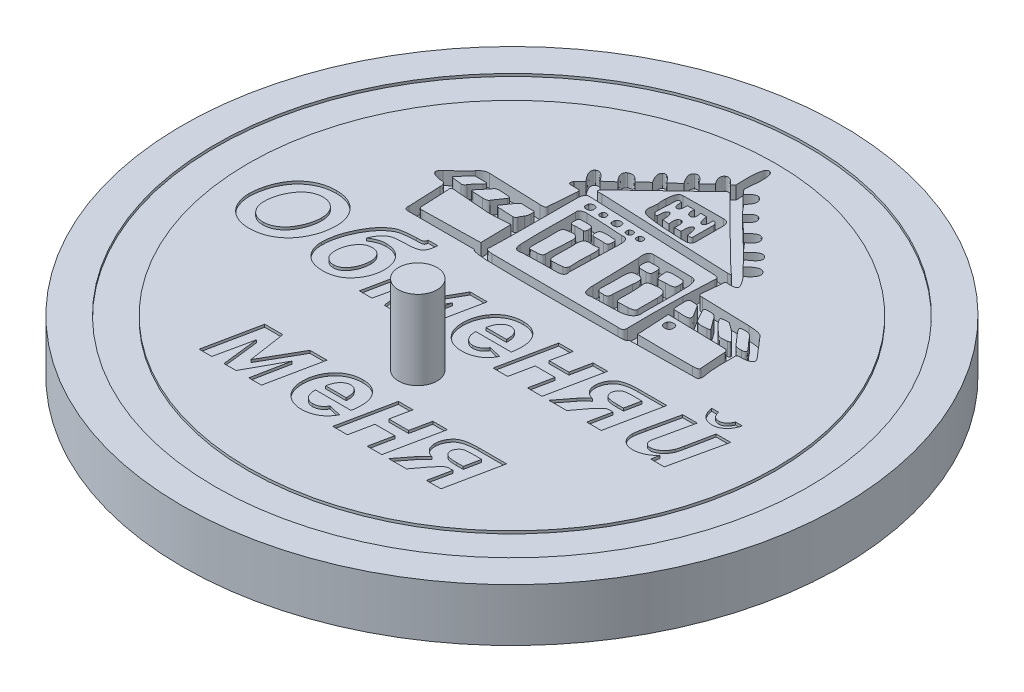
SolidWorks part; units mm, degrees
ref_plane "Спереди" through (0, 0, 0) normal (0, 0, 1) x (1, 0, 0)
ref_plane "Сверху" through (0, 0, 0) normal (0, 1, 0) x (1, 0, 0)
ref_plane "Справа" through (0, 0, 0) normal (1, 0, 0) x (0, 0, -1)
sketch "Эскиз1" plane through (0, 0, 0) normal (0, 1, 0) x (1, 0, 0)
  circle A0 centre (0, 0) radius 25
  dimension "D1" = 50
extrude "Бобышка-Вытянуть1" add sketch "Эскиз1" along normal blind 4
sketch "Эскиз2" plane through (0, 4, 0) normal (0, 1, 0) x (1, 0, 0)
  circle A0 centre (0, 0) radius 22.5
  circle A1 centre (0, 0) radius 20
  dimension "D1" = 45
  dimension "D2" = 40
extrude "Вырез-Вытянуть1" cut sketch "Эскиз2" against normal blind 0.2
sketch "Эскиз3" plane through (0, 4, 0) normal (0, 1, 0) x (1, 0, 0)
  text T0 "<b>Обменяй </b>\r\n<b>    меня</b>" font "Arial" height in points 22
extrude "Вырез-Вытянуть2" cut sketch "Эскиз3" against normal blind 0.2
sketch "Эскиз4" plane through (0, 4, 0) normal (0, 1, 0) x (1, 0, 0)
  line B0 (6.0558, 2.8211) -> (10.9499, 2.8913)
  line B1 (5.5647, 11.9601) -> (5.135, 12.46)
  line B2 (4.6263, 12.9249) -> (4.0299, 13.6177)
  line B3 (3.3984, 14.1615) -> (2.6617, 14.8719)
  line B4 (2.1004, 15.3718) -> (1.4776, 16.0998)
  line B5 (0.8198, 16.7226) -> (0.4953, 17.0997)
  line B6 (-0.0835, 17.0821) -> (-0.3116, 16.8804)
  line B7 (-0.9255, 16.3629) -> (-1.557, 15.7402)
  line B8 (-2.1534, 15.2052) -> (-2.8463, 14.5913)
  line B9 (-3.4252, 14.0826) -> (-4.1268, 13.4599)
  line B10 (-4.767, 12.8021) -> (-5.495, 12.1706)
  line B11 (-5.9949, 11.6093) -> (-6.451, 11.162)
  line B12 (-9.6874, 6.8425) -> (-9.0427, 7.6274)
  line B13 (-7.6701, 6.5969) -> (-6.4422, 6.5311)
  line B14 (5.9946, 3.536) -> (5.8542, 6.0093)
  line B15 (5.8542, 6.0093) -> (10.3097, 5.904)
  line B16 (-10.6872, 5.8426) -> (-10.5907, 3.7026)
  line B17 (-5.9774, 3.6149) -> (-6.0212, 5.9478)
  line B18 (-0.5858, 12.0196) -> (-0.0683, 11.9757)
  line B19 (0.3702, 11.9318) -> (0.8702, 11.9494)
  line B20 (0.8965, 13.8701) -> (0.4316, 13.8789)
  line B21 (-0.0332, 13.8789) -> (-0.5682, 13.8701)
  line B22 (-3.5064, 8.2833) -> (-2.8661, 8.2833)
  spline B23 degree 2 poles (-11.6257, 6.2066) (-11.2047, 6.2416) (-11.2047, 5.7505) knots 0 0 0 0.015873 0.015873 0.015873
  spline B24 degree 2 poles (-11.2047, 5.7505) (-11.2047, 5.2593) (-11.0994, 3.2947) knots 0.015873 0.015873 0.015873 0.031746 0.031746 0.031746
  spline B25 degree 2 poles (-11.0994, 3.2947) (-11.1696, 2.9088) (-10.7662, 2.9263) knots 0.031746 0.031746 0.031746 0.047619 0.047619 0.047619
  spline B26 degree 2 poles (-10.7662, 2.9263) (-10.3627, 2.9439) (-5.7494, 2.9263) knots 0.047619 0.047619 0.047619 0.063492 0.063492 0.063492
  spline B27 degree 2 poles (-5.7494, 2.9263) (-5.802, 2.7509) (-4.6267, 2.6808) knots 0.063492 0.063492 0.063492 0.079365 0.079365 0.079365
  spline B28 degree 2 poles (-4.6267, 2.6808) (-3.4515, 2.6106) (5.5121, 2.6457) knots 0.079365 0.079365 0.079365 0.095238 0.095238 0.095238
  spline B29 degree 2 poles (5.5121, 2.6457) (6.0383, 2.6281) (6.0558, 2.8211) knots 0.095238 0.095238 0.095238 0.111111 0.111111 0.111111
  spline B30 degree 2 poles (10.9499, 2.8913) (11.3884, 2.8211) (11.2481, 3.4526) knots 0.126984 0.126984 0.126984 0.142857 0.142857 0.142857
  spline B31 degree 2 poles (11.2481, 3.4526) (11.1077, 4.0841) (11.1428, 5.6453) knots 0.142857 0.142857 0.142857 0.15873 0.15873 0.15873
  spline B32 degree 2 poles (11.1428, 5.6453) (11.0551, 5.9347) (11.3358, 5.9259) knots 0.15873 0.15873 0.15873 0.174603 0.174603 0.174603
  spline B33 degree 3 poles (11.3358, 5.9259) (11.6164, 5.9171) (12.5636, 5.9698) (12.0901, 6.5135) knots 0.174603 0.174603 0.174603 0.174603 0.190476 0.190476 0.190476 0.190476
  spline B34 degree 2 poles (12.0901, 6.5135) (11.6164, 7.0573) (10.8359, 7.9695) knots 0.190476 0.190476 0.190476 0.206349 0.206349 0.206349
  spline B35 degree 2 poles (10.8359, 7.9695) (10.7131, 8.2852) (9.6606, 8.3203) knots 0.206349 0.206349 0.206349 0.222222 0.222222 0.222222
  spline B36 degree 2 poles (9.6606, 8.3203) (8.6081, 8.3554) (6.012, 8.4255) knots 0.222222 0.222222 0.222222 0.238095 0.238095 0.238095
  spline B37 degree 2 poles (6.012, 8.4255) (5.7226, 8.3729) (5.7401, 8.6711) knots 0.238095 0.238095 0.238095 0.253968 0.253968 0.253968
  spline B38 degree 2 poles (5.7401, 8.6711) (5.7577, 8.9693) (5.8893, 10.1797) knots 0.253968 0.253968 0.253968 0.269841 0.269841 0.269841
  spline B39 degree 2 poles (5.8893, 10.1797) (5.8717, 10.2937) (6.0384, 10.2937) knots 0.269841 0.269841 0.269841 0.285714 0.285714 0.285714
  spline B40 degree 3 poles (6.0384, 10.2937) (6.205, 10.2937) (6.9943, 10.1797) (6.6698, 10.6971) knots 0.285714 0.285714 0.285714 0.285714 0.301587 0.301587 0.301587 0.301587
  spline B41 degree 2 poles (6.6698, 10.6971) (6.3453, 11.2146) (6.205, 11.3286) knots 0.301587 0.301587 0.301587 0.31746 0.31746 0.31746
  spline B42 degree 2 poles (6.205, 11.3286) (7.0294, 11.9864) (6.6786, 12.3635) knots 0.31746 0.31746 0.31746 0.333333 0.333333 0.333333
  spline B43 degree 2 poles (6.6786, 12.3635) (6.3278, 12.7406) (5.5647, 11.9601) knots 0.333333 0.333333 0.333333 0.349206 0.349206 0.349206
  spline B44 degree 2 poles (5.135, 12.46) (6.091, 13.0389) (5.7401, 13.4248) knots 0.365079 0.365079 0.365079 0.380952 0.380952 0.380952
  spline B45 degree 2 poles (5.7401, 13.4248) (5.3893, 13.8106) (4.6263, 12.9249) knots 0.380952 0.380952 0.380952 0.396825 0.396825 0.396825
  spline B46 degree 2 poles (4.0299, 13.6177) (4.7754, 14.1176) (4.4246, 14.5386) knots 0.412698 0.412698 0.412698 0.428571 0.428571 0.428571
  spline B47 degree 2 poles (4.4246, 14.5386) (4.0737, 14.9596) (3.3984, 14.1615) knots 0.428571 0.428571 0.428571 0.444444 0.444444 0.444444
  spline B48 degree 2 poles (2.6617, 14.8719) (3.3019, 15.4332) (2.9774, 15.7577) knots 0.460317 0.460317 0.460317 0.47619 0.47619 0.47619
  spline B49 degree 2 poles (2.9774, 15.7577) (2.6529, 16.0823) (2.1004, 15.3718) knots 0.47619 0.47619 0.47619 0.492063 0.492063 0.492063
  spline B50 degree 2 poles (1.4776, 16.0998) (2.0565, 16.6348) (1.7408, 17.0383) knots 0.507937 0.507937 0.507937 0.52381 0.52381 0.52381
  spline B51 degree 2 poles (1.7408, 17.0383) (1.425, 17.4417) (0.8198, 16.7226) knots 0.52381 0.52381 0.52381 0.539683 0.539683 0.539683
  spline B52 degree 2 poles (0.4953, 17.0997) (0.776, 19.1871) (0.2848, 19.2572) knots 0.555556 0.555556 0.555556 0.571429 0.571429 0.571429
  spline B53 degree 2 poles (0.2848, 19.2572) (-0.2063, 19.3274) (-0.0835, 17.0821) knots 0.571429 0.571429 0.571429 0.587302 0.587302 0.587302
  spline B54 degree 2 poles (-0.3116, 16.8804) (-0.7852, 17.468) (-1.0834, 17.2312) knots 0.603175 0.603175 0.603175 0.619048 0.619048 0.619048
  spline B55 degree 2 poles (-1.0834, 17.2312) (-1.3816, 16.9944) (-0.9255, 16.3629) knots 0.619048 0.619048 0.619048 0.634921 0.634921 0.634921
  spline B56 degree 2 poles (-1.557, 15.7402) (-2.0482, 16.4857) (-2.3902, 16.2401) knots 0.650794 0.650794 0.650794 0.666667 0.666667 0.666667
  spline B57 degree 2 poles (-2.3902, 16.2401) (-2.7323, 15.9946) (-2.1534, 15.2052) knots 0.666667 0.666667 0.666667 0.68254 0.68254 0.68254
  spline B58 degree 2 poles (-2.8463, 14.5913) (-3.355, 15.2929) (-3.6356, 15.0649) knots 0.698413 0.698413 0.698413 0.714286 0.714286 0.714286
  spline B59 degree 2 poles (-3.6356, 15.0649) (-3.9163, 14.8368) (-3.4252, 14.0826) knots 0.714286 0.714286 0.714286 0.730159 0.730159 0.730159
  spline B60 degree 2 poles (-4.1268, 13.4599) (-4.6004, 14.0299) (-5.0039, 13.7581) knots 0.746032 0.746032 0.746032 0.761905 0.761905 0.761905
  spline B61 degree 2 poles (-5.0039, 13.7581) (-5.4073, 13.4862) (-4.767, 12.8021) knots 0.761905 0.761905 0.761905 0.777778 0.777778 0.777778
  spline B62 degree 2 poles (-5.495, 12.1706) (-6.0388, 12.9775) (-6.3896, 12.7144) knots 0.793651 0.793651 0.793651 0.809524 0.809524 0.809524
  spline B63 degree 2 poles (-6.3896, 12.7144) (-6.7405, 12.4513) (-5.9949, 11.6093) knots 0.809524 0.809524 0.809524 0.825397 0.825397 0.825397
  spline B64 degree 2 poles (-6.451, 11.162) (-6.6615, 10.8287) (-6.3107, 10.8199) knots 0.84127 0.84127 0.84127 0.857143 0.857143 0.857143
  spline B65 degree 2 poles (-6.3107, 10.8199) (-5.9599, 10.8111) (-5.7494, 10.8111) knots 0.857143 0.857143 0.857143 0.873016 0.873016 0.873016
  spline B66 degree 2 poles (-5.7494, 10.8111) (-5.6178, 10.7936) (-5.6441, 10.5656) knots 0.873016 0.873016 0.873016 0.888889 0.888889 0.888889
  spline B67 degree 2 poles (-5.6441, 10.5656) (-5.6705, 10.3375) (-5.8108, 8.5483) knots 0.888889 0.888889 0.888889 0.904762 0.904762 0.904762
  spline B68 degree 2 poles (-5.8108, 8.5483) (-5.7581, 8.3203) (-6.2318, 8.3554) knots 0.904762 0.904762 0.904762 0.920635 0.920635 0.920635
  spline B69 degree 2 poles (-6.2318, 8.3554) (-6.7054, 8.3905) (-10.2136, 8.5045) knots 0.920635 0.920635 0.920635 0.936508 0.936508 0.936508
  spline B70 degree 2 poles (-10.2136, 8.5045) (-10.6171, 8.5132) (-10.9065, 8.1273) knots 0.936508 0.936508 0.936508 0.952381 0.952381 0.952381
  spline B71 degree 2 poles (-10.9065, 8.1273) (-11.1959, 7.7414) (-12.1607, 6.9257) knots 0.952381 0.952381 0.952381 0.968254 0.968254 0.968254
  spline B72 degree 2 poles (-12.1607, 6.9257) (-12.7571, 6.3644) (-11.6257, 6.2066) knots 0.968254 0.968254 0.968254 1 1 1
  spline B73 degree 2 poles (-11.2573, 7.0222) (-11.4854, 6.8424) (-11.2793, 6.8074) knots 0 0 0 0.111111 0.111111 0.111111
  spline B74 degree 2 poles (-11.2793, 6.8074) (-11.0731, 6.7723) (-10.5951, 6.7284) knots 0.111111 0.111111 0.111111 0.222222 0.222222 0.222222
  spline B75 degree 2 poles (-10.5951, 6.7284) (-10.446, 6.6802) (-10.3013, 6.9082) knots 0.222222 0.222222 0.222222 0.333333 0.333333 0.333333
  spline B76 degree 2 poles (-10.3013, 6.9082) (-10.1566, 7.1363) (-9.7532, 7.5572) knots 0.333333 0.333333 0.333333 0.444444 0.444444 0.444444
  spline B77 degree 2 poles (-9.7532, 7.5572) (-9.547, 7.7546) (-9.7575, 7.7678) knots 0.444444 0.444444 0.444444 0.555556 0.555556 0.555556
  spline B78 degree 2 poles (-9.7575, 7.7678) (-9.968, 7.7809) (-10.4592, 7.7721) knots 0.555556 0.555556 0.555556 0.666667 0.666667 0.666667
  spline B79 degree 2 poles (-10.4592, 7.7721) (-10.5381, 7.8072) (-10.6477, 7.7063) knots 0.666667 0.666667 0.666667 0.777778 0.777778 0.777778
  spline B80 degree 2 poles (-10.6477, 7.7063) (-10.7574, 7.6055) (-11.2573, 7.0222) knots 0.777778 0.777778 0.777778 1 1 1
  spline B81 degree 2 poles (-9.0427, 7.6274) (-8.9945, 7.7458) (-8.7139, 7.7546) knots 0.111111 0.111111 0.111111 0.222222 0.222222 0.222222
  spline B82 degree 2 poles (-8.7139, 7.7546) (-8.4332, 7.7634) (-8.0692, 7.7151) knots 0.222222 0.222222 0.222222 0.333333 0.333333 0.333333
  spline B83 degree 2 poles (-8.0692, 7.7151) (-7.7491, 7.7107) (-7.8806, 7.5266) knots 0.333333 0.333333 0.333333 0.444444 0.444444 0.444444
  spline B84 degree 2 poles (-7.8806, 7.5266) (-8.0122, 7.3424) (-8.4112, 6.7504) knots 0.444444 0.444444 0.444444 0.555556 0.555556 0.555556
  spline B85 degree 2 poles (-8.4112, 6.7504) (-8.442, 6.61) (-8.8322, 6.6144) knots 0.555556 0.555556 0.555556 0.666667 0.666667 0.666667
  spline B86 degree 2 poles (-8.8322, 6.6144) (-9.2225, 6.6188) (-9.6216, 6.6539) knots 0.666667 0.666667 0.666667 0.777778 0.777778 0.777778
  spline B87 degree 2 poles (-9.6216, 6.6539) (-9.8584, 6.6758) (-9.6874, 6.8425) knots 0.777778 0.777778 0.777778 1 1 1
  spline B88 degree 2 poles (-6.4422, 6.5311) (-6.2887, 6.5618) (-6.2405, 6.6934) knots 0.1 0.1 0.1 0.2 0.2 0.2
  spline B89 degree 2 poles (-6.2405, 6.6934) (-6.1923, 6.8249) (-6.0607, 7.0222) knots 0.2 0.2 0.2 0.3 0.3 0.3
  spline B90 degree 2 poles (-6.0607, 7.0222) (-5.9642, 7.1977) (-5.9599, 7.395) knots 0.3 0.3 0.3 0.4 0.4 0.4
  spline B91 degree 3 poles (-5.9599, 7.395) (-5.9555, 7.5923) (-5.8941, 7.7107) (-6.1528, 7.6976) knots 0.4 0.4 0.4 0.4 0.5 0.5 0.5 0.5
  spline B92 degree 2 poles (-6.1528, 7.6976) (-6.4116, 7.6844) (-6.9246, 7.7195) knots 0.5 0.5 0.5 0.6 0.6 0.6
  spline B93 degree 2 poles (-6.9246, 7.7195) (-7.0167, 7.7502) (-7.1439, 7.6099) knots 0.6 0.6 0.6 0.7 0.7 0.7
  spline B94 degree 2 poles (-7.1439, 7.6099) (-7.2711, 7.4696) (-7.7447, 6.7591) knots 0.7 0.7 0.7 0.8 0.8 0.8
  spline B95 degree 2 poles (-7.7447, 6.7591) (-7.8192, 6.6363) (-7.6701, 6.5969) knots 0.8 0.8 0.8 1 1 1
  spline B96 degree 3 poles (6.0799, 6.538) (6.571, 6.5157) (7.2003, 6.3978) (6.8254, 6.9765) knots 0 0 0 0 0.166667 0.166667 0.166667 0.166667
  spline B97 degree 3 poles (6.8254, 6.9765) (6.4792, 7.5109) (6.5009, 7.5027) (6.4395, 7.5992) knots 0.166667 0.166667 0.166667 0.166667 0.333333 0.333333 0.333333 0.333333
  spline B98 degree 3 poles (6.4395, 7.5992) (6.3781, 7.6957) (6.3781, 7.7308) (6.0799, 7.7395) knots 0.333333 0.333333 0.333333 0.333333 0.5 0.5 0.5 0.5
  spline B99 degree 3 poles (6.0799, 7.7395) (5.7356, 7.7497) (5.615, 7.8845) (5.6451, 7.1604) knots 0.5 0.5 0.5 0.5 0.666667 0.666667 0.666667 0.666667
  spline B100 degree 3 poles (5.6451, 7.1604) (5.676, 6.419) (5.6735, 6.5564) (6.0799, 6.538) knots 0.666667 0.666667 0.666667 0.666667 1 1 1 1
  spline B101 degree 3 poles (7.1587, 7.0861) (7.0857, 7.2532) (6.956, 7.3736) (6.8829, 7.6243) knots 0 0 0 0 0.111111 0.111111 0.111111 0.111111
  spline B102 degree 3 poles (6.8829, 7.6243) (6.8553, 7.7188) (6.931, 7.7486) (7.0798, 7.7571) knots 0.111111 0.111111 0.111111 0.111111 0.222222 0.222222 0.222222 0.222222
  spline B103 degree 3 poles (7.0798, 7.7571) (7.3868, 7.7746) (7.3868, 7.7395) (7.492, 7.7308) knots 0.222222 0.222222 0.222222 0.222222 0.333333 0.333333 0.333333 0.333333
  spline B104 degree 3 poles (7.492, 7.7308) (7.5972, 7.722) (7.6674, 7.722) (7.9481, 7.3186) knots 0.333333 0.333333 0.333333 0.333333 0.444444 0.444444 0.444444 0.444444
  spline B105 degree 2 poles (7.9481, 7.3186) (8.2287, 6.9151) (8.3691, 6.7485) knots 0.444444 0.444444 0.444444 0.555556 0.555556 0.555556
  spline B106 degree 2 poles (8.3691, 6.7485) (8.562, 6.5731) (8.2375, 6.5467) knots 0.555556 0.555556 0.555556 0.666667 0.666667 0.666667
  spline B107 degree 3 poles (8.2375, 6.5467) (8.0005, 6.5275) (7.7297, 6.5102) (7.5924, 6.5591) knots 0.666667 0.666667 0.666667 0.666667 0.777778 0.777778 0.777778 0.777778
  spline B108 degree 3 poles (7.5924, 6.5591) (7.4028, 6.6265) (7.3148, 6.7562) (7.1587, 7.0861) knots 0.777778 0.777778 0.777778 0.777778 1 1 1 1
  spline B109 degree 3 poles (8.1207, 7.6044) (8.0402, 7.7449) (8.169, 7.7427) (8.3427, 7.7658) knots 0 0 0 0 0.142857 0.142857 0.142857 0.142857
  spline B110 degree 2 poles (8.3427, 7.7658) (8.7374, 7.8185) (8.7725, 7.7308) knots 0.142857 0.142857 0.142857 0.285714 0.285714 0.285714
  spline B111 degree 2 poles (8.7725, 7.7308) (9.2637, 7.4063) (9.6145, 7.0554) knots 0.285714 0.285714 0.285714 0.428571 0.428571 0.428571
  spline B112 degree 3 poles (9.6145, 7.0554) (9.9653, 6.7046) (10.1714, 6.5174) (9.8688, 6.4941) knots 0.428571 0.428571 0.428571 0.428571 0.571429 0.571429 0.571429 0.571429
  spline B113 degree 3 poles (9.8688, 6.4941) (9.4039, 6.4583) (9.2888, 6.3801) (8.9884, 6.6721) knots 0.571429 0.571429 0.571429 0.571429 0.714286 0.714286 0.714286 0.714286
  spline B114 degree 3 poles (8.9884, 6.6721) (8.6449, 7.0061) (8.3252, 7.2481) (8.1207, 7.6044) knots 0.714286 0.714286 0.714286 0.714286 1 1 1 1
  spline B115 degree 3 poles (9.5095, 7.8173) (9.632, 7.8792) (10.0231, 7.8626) (10.1326, 7.8217) knots 0 0 0 0 0.166667 0.166667 0.166667 0.166667
  spline B116 degree 3 poles (10.1326, 7.8217) (10.3502, 7.7403) (10.5713, 7.4128) (10.7284, 7.2221) knots 0.166667 0.166667 0.166667 0.166667 0.333333 0.333333 0.333333 0.333333
  spline B117 degree 3 poles (10.7284, 7.2221) (10.9739, 6.9239) (11.5923, 6.459) (11.0003, 6.4239) knots 0.333333 0.333333 0.333333 0.333333 0.5 0.5 0.5 0.5
  spline B118 degree 3 poles (11.0003, 6.4239) (10.4082, 6.3889) (10.3364, 6.6793) (10.2591, 6.7748) knots 0.5 0.5 0.5 0.5 0.666667 0.666667 0.666667 0.666667
  spline B119 degree 3 poles (10.2591, 6.7748) (10.1819, 6.8702) (9.3192, 7.721) (9.5095, 7.8173) knots 0.666667 0.666667 0.666667 0.666667 1 1 1 1
  spline B120 degree 2 poles (-5.3108, 3.6061) (-5.4161, 3.3342) (-4.8021, 3.3079) knots 0 0 0 0.1 0.1 0.1
  spline B121 degree 2 poles (-4.8021, 3.3079) (-4.1882, 3.2816) (4.8017, 3.2553) knots 0.1 0.1 0.1 0.2 0.2 0.2
  spline B122 degree 2 poles (4.8017, 3.2553) (5.2402, 3.1851) (5.2052, 3.571) knots 0.2 0.2 0.2 0.3 0.3 0.3
  spline B123 degree 3 poles (5.2052, 3.571) (5.1701, 3.9569) (5.1876, 6.974) (5.2227, 7.7634) knots 0.3 0.3 0.3 0.3 0.4 0.4 0.4 0.4
  spline B124 degree 2 poles (5.2227, 7.7634) (5.2578, 8.5527) (5.328, 10.0613) knots 0.4 0.4 0.4 0.5 0.5 0.5
  spline B125 degree 2 poles (5.328, 10.0613) (5.4157, 10.3419) (4.9596, 10.3595) knots 0.5 0.5 0.5 0.6 0.6 0.6
  spline B126 degree 2 poles (4.9596, 10.3595) (4.5035, 10.377) (-4.8109, 10.7629) knots 0.6 0.6 0.6 0.7 0.7 0.7
  spline B127 degree 2 poles (-4.8109, 10.7629) (-5.2319, 10.8331) (-5.2494, 10.1841) knots 0.7 0.7 0.7 0.8 0.8 0.8
  spline B128 degree 3 poles (-5.2494, 10.1841) (-5.267, 9.535) (-5.2319, 4.8866) (-5.3108, 3.6061) knots 0.8 0.8 0.8 0.8 1 1 1 1
  spline B129 degree 2 poles (-4.5676, 11.4056) (-5.164, 11.3004) (-4.8307, 11.6687) knots 0 0 0 0.142857 0.142857 0.142857
  spline B130 degree 2 poles (-4.8307, 11.6687) (-4.4974, 12.0371) (-0.1121, 16.1593) knots 0.142857 0.142857 0.142857 0.285714 0.285714 0.285714
  spline B131 degree 2 poles (-0.1121, 16.1593) (0.0984, 16.4926) (0.379, 16.1593) knots 0.285714 0.285714 0.285714 0.428571 0.428571 0.428571
  spline B132 degree 2 poles (0.379, 16.1593) (0.6597, 15.826) (5.4309, 11.1776) knots 0.428571 0.428571 0.428571 0.571429 0.571429 0.571429
  spline B133 degree 2 poles (5.4309, 11.1776) (5.7817, 10.9671) (5.3783, 10.9671) knots 0.571429 0.571429 0.571429 0.714286 0.714286 0.714286
  spline B134 degree 2 poles (5.3783, 10.9671) (4.9748, 10.9671) (-4.5676, 11.4056) knots 0.714286 0.714286 0.714286 1 1 1
  spline B135 degree 2 poles (10.3097, 5.904) (10.4851, 5.8339) (10.4851, 5.6409) knots 0.285714 0.285714 0.285714 0.428571 0.428571 0.428571
  spline B136 degree 2 poles (10.4851, 5.6409) (10.4851, 5.448) (10.6255, 3.7289) knots 0.428571 0.428571 0.428571 0.571429 0.571429 0.571429
  spline B137 degree 2 poles (10.6255, 3.7289) (10.6956, 3.5184) (10.1694, 3.5184) knots 0.571429 0.571429 0.571429 0.714286 0.714286 0.714286
  spline B138 degree 3 poles (10.1694, 3.5184) (9.6431, 3.5184) (6.6962, 3.4834) (5.9946, 3.536) knots 0.714286 0.714286 0.714286 0.714286 1 1 1 1
  spline B139 degree 2 poles (-10.5907, 3.7026) (-10.5907, 3.5359) (-10.3363, 3.5272) knots 0.125 0.125 0.125 0.25 0.25 0.25
  spline B140 degree 2 poles (-10.3363, 3.5272) (-10.082, 3.5184) (-5.9774, 3.6149) knots 0.25 0.25 0.25 0.375 0.375 0.375
  spline B141 degree 2 poles (-6.0212, 5.9478) (-7.1702, 5.8426) (-7.7052, 5.8601) knots 0.5 0.5 0.5 0.625 0.625 0.625
  spline B142 degree 3 poles (-7.7052, 5.8601) (-8.2402, 5.8777) (-10.1347, 6.0443) (-10.2487, 6.0618) knots 0.625 0.625 0.625 0.625 0.75 0.75 0.75 0.75
  spline B143 degree 3 poles (-10.2487, 6.0618) (-10.3627, 6.0794) (-10.7837, 6.1846) (-10.6872, 5.8426) knots 0.75 0.75 0.75 0.75 1 1 1 1
  spline B144 degree 2 poles (6.3103, 5.448) (6.17, 4.9743) (6.6261, 4.9743) knots 0 0 0 0.25 0.25 0.25
  spline B145 degree 3 poles (6.6261, 4.9743) (7.0821, 4.9743) (6.9769, 5.5006) (6.8453, 5.5795) knots 0.25 0.25 0.25 0.25 0.5 0.5 0.5 0.5
  spline B146 degree 3 poles (6.8453, 5.5795) (6.7137, 5.6584) (6.3805, 5.6584) (6.3103, 5.448) knots 0.5 0.5 0.5 0.5 1 1 1 1
  spline B147 degree 2 poles (-0.3879, 10.0048) (-0.4848, 9.6777) (-0.1698, 9.6777) knots 0 0 0 0.25 0.25 0.25
  spline B148 degree 3 poles (-0.1698, 9.6777) (0.1452, 9.6777) (0.0725, 10.0411) (-0.0183, 10.0957) knots 0.25 0.25 0.25 0.25 0.5 0.5 0.5 0.5
  spline B149 degree 3 poles (-0.0183, 10.0957) (-0.1092, 10.1502) (-0.3394, 10.1502) (-0.3879, 10.0048) knots 0.5 0.5 0.5 0.5 1 1 1 1
  spline B150 degree 2 poles (-1.1948, 10.0223) (-1.2917, 9.6952) (-0.9767, 9.6952) knots 0 0 0 0.25 0.25 0.25
  spline B151 degree 3 poles (-0.9767, 9.6952) (-0.6617, 9.6952) (-0.7344, 10.0587) (-0.8252, 10.1132) knots 0.25 0.25 0.25 0.25 0.5 0.5 0.5 0.5
  spline B152 degree 3 poles (-0.8252, 10.1132) (-0.9161, 10.1677) (-1.1463, 10.1677) (-1.1948, 10.0223) knots 0.5 0.5 0.5 0.5 1 1 1 1
  spline B153 degree 2 poles (-2.3313, 10.1601) (-2.4534, 9.7478) (-2.0565, 9.7478) knots 0 0 0 0.25 0.25 0.25
  spline B154 degree 3 poles (-2.0565, 9.7478) (-1.6595, 9.7478) (-1.7511, 10.2059) (-1.8656, 10.2745) knots 0.25 0.25 0.25 0.25 0.5 0.5 0.5 0.5
  spline B155 degree 3 poles (-1.8656, 10.2745) (-1.9801, 10.3432) (-2.2702, 10.3432) (-2.3313, 10.1601) knots 0.5 0.5 0.5 0.5 1 1 1 1
  spline B156 degree 2 poles (-3.3523, 10.1802) (-3.4492, 9.8531) (-3.1342, 9.8531) knots 0 0 0 0.25 0.25 0.25
  spline B157 degree 3 poles (-3.1342, 9.8531) (-2.8193, 9.8531) (-2.8919, 10.2166) (-2.9828, 10.2711) knots 0.25 0.25 0.25 0.25 0.5 0.5 0.5 0.5
  spline B158 degree 3 poles (-2.9828, 10.2711) (-3.0737, 10.3256) (-3.3039, 10.3256) (-3.3523, 10.1802) knots 0.5 0.5 0.5 0.5 1 1 1 1
  spline B159 degree 2 poles (-4.419, 10.223) (-4.539, 9.818) (-4.149, 9.818) knots 0 0 0 0.25 0.25 0.25
  spline B160 degree 3 poles (-4.149, 9.818) (-3.759, 9.818) (-3.849, 10.268) (-3.9615, 10.3355) knots 0.25 0.25 0.25 0.25 0.5 0.5 0.5 0.5
  spline B161 degree 3 poles (-3.9615, 10.3355) (-4.074, 10.403) (-4.359, 10.403) (-4.419, 10.223) knots 0.5 0.5 0.5 0.5 1 1 1 1
  spline B162 degree 2 poles (-1.8312, 13.5281) (-1.8136, 14.3525) (-1.3926, 14.3701) knots 0 0 0 0.111111 0.111111 0.111111
  spline B163 degree 2 poles (-1.3926, 14.3701) (-0.9717, 14.3876) (1.6595, 14.3876) knots 0.111111 0.111111 0.111111 0.222222 0.222222 0.222222
  spline B164 degree 2 poles (1.6595, 14.3876) (2.1156, 14.4052) (2.1332, 13.8614) knots 0.222222 0.222222 0.222222 0.333333 0.333333 0.333333
  spline B165 degree 2 poles (2.1332, 13.8614) (2.1507, 13.3176) (2.1332, 11.9318) knots 0.333333 0.333333 0.333333 0.444444 0.444444 0.444444
  spline B166 degree 2 poles (2.1332, 11.9318) (2.1682, 11.5109) (1.7823, 11.4582) knots 0.444444 0.444444 0.444444 0.555556 0.555556 0.555556
  spline B167 degree 3 poles (1.7823, 11.4582) (1.3964, 11.4056) (-0.6033, 11.5284) (-1.3751, 11.6863) knots 0.555556 0.555556 0.555556 0.555556 0.666667 0.666667 0.666667 0.666667
  spline B168 degree 3 poles (-1.3751, 11.6863) (-2.1469, 11.8441) (-1.761, 12.5458) (-1.8136, 12.8966) knots 0.666667 0.666667 0.666667 0.666667 0.777778 0.777778 0.777778 0.777778
  spline B169 degree 2 poles (-1.8136, 12.8966) (-1.8662, 13.2475) (-1.8312, 13.5281) knots 0.777778 0.777778 0.777778 1 1 1
  spline B170 degree 2 poles (-1.0155, 13.8789) (-1.2874, 13.9579) (-1.3049, 13.7561) knots 0 0 0 0.043478 0.043478 0.043478
  spline B171 degree 2 poles (-1.3049, 13.7561) (-1.3225, 13.5544) (-1.3663, 12.4844) knots 0.043478 0.043478 0.043478 0.086957 0.086957 0.086957
  spline B172 degree 2 poles (-1.3663, 12.4844) (-1.4278, 12.0371) (-1.0506, 12.0634) knots 0.086957 0.086957 0.086957 0.130435 0.130435 0.130435
  spline B173 degree 2 poles (-1.0506, 12.0634) (-1.0681, 12.7563) (-0.8138, 12.7563) knots 0.130435 0.130435 0.130435 0.173913 0.173913 0.173913
  spline B174 degree 2 poles (-0.8138, 12.7563) (-0.5594, 12.7563) (-0.5858, 12.0196) knots 0.173913 0.173913 0.173913 0.217391 0.217391 0.217391
  spline B175 degree 2 poles (-0.0683, 11.9757) (-0.1823, 12.651) (0.1422, 12.6774) knots 0.26087 0.26087 0.26087 0.304348 0.304348 0.304348
  spline B176 degree 2 poles (0.1422, 12.6774) (0.4667, 12.7037) (0.3702, 11.9318) knots 0.304348 0.304348 0.304348 0.347826 0.347826 0.347826
  spline B177 degree 2 poles (0.8702, 11.9494) (0.8614, 12.7037) (1.0894, 12.7037) knots 0.391304 0.391304 0.391304 0.434783 0.434783 0.434783
  spline B178 degree 2 poles (1.0894, 12.7037) (1.3175, 12.7037) (1.3876, 11.9318) knots 0.434783 0.434783 0.434783 0.478261 0.478261 0.478261
  spline B179 degree 2 poles (1.3876, 11.9318) (1.7034, 11.8792) (1.7034, 12.0196) knots 0.478261 0.478261 0.478261 0.521739 0.521739 0.521739
  spline B180 degree 2 poles (1.7034, 12.0196) (1.7034, 12.1599) (1.7209, 13.5807) knots 0.521739 0.521739 0.521739 0.565217 0.565217 0.565217
  spline B181 degree 2 poles (1.7209, 13.5807) (1.6771, 13.8789) (1.4052, 13.8526) knots 0.565217 0.565217 0.565217 0.608696 0.608696 0.608696
  spline B182 degree 2 poles (1.4052, 13.8526) (1.4402, 13.1948) (1.1947, 13.2036) knots 0.608696 0.608696 0.608696 0.652174 0.652174 0.652174
  spline B183 degree 2 poles (1.1947, 13.2036) (0.9491, 13.2124) (0.8965, 13.8701) knots 0.652174 0.652174 0.652174 0.695652 0.695652 0.695652
  spline B184 degree 2 poles (0.4316, 13.8789) (0.5807, 13.2913) (0.2387, 13.2825) knots 0.73913 0.73913 0.73913 0.782609 0.782609 0.782609
  spline B185 degree 2 poles (0.2387, 13.2825) (-0.1034, 13.2737) (-0.0332, 13.8789) knots 0.782609 0.782609 0.782609 0.826087 0.826087 0.826087
  spline B186 degree 2 poles (-0.5682, 13.8701) (-0.5331, 13.3176) (-0.7787, 13.3) knots 0.869565 0.869565 0.869565 0.913043 0.913043 0.913043
  spline B187 degree 2 poles (-0.7787, 13.3) (-1.0243, 13.2825) (-1.0155, 13.8789) knots 0.913043 0.913043 0.913043 1 1 1
  spline B188 degree 2 poles (-4.3746, 9.1779) (-4.4624, 9.5463) (-3.8835, 9.5638) knots 0 0 0 0.111111 0.111111 0.111111
  spline B189 degree 2 poles (-3.8835, 9.5638) (-3.3046, 9.5814) (-1.0944, 9.4235) knots 0.111111 0.111111 0.111111 0.222222 0.222222 0.222222
  spline B190 degree 2 poles (-1.0944, 9.4235) (-0.5507, 9.5463) (-0.5858, 8.7394) knots 0.222222 0.222222 0.222222 0.333333 0.333333 0.333333
  spline B191 degree 2 poles (-0.5858, 8.7394) (-0.6208, 7.9325) (-0.691, 5.0557) knots 0.333333 0.333333 0.333333 0.444444 0.444444 0.444444
  spline B192 degree 2 poles (-0.691, 5.0557) (-0.5331, 4.547) (-1.2348, 4.5646) knots 0.444444 0.444444 0.444444 0.555556 0.555556 0.555556
  spline B193 degree 2 poles (-1.2348, 4.5646) (-1.9364, 4.5821) (-3.7432, 4.5119) knots 0.555556 0.555556 0.555556 0.666667 0.666667 0.666667
  spline B194 degree 2 poles (-3.7432, 4.5119) (-4.287, 4.3365) (-4.3571, 4.9504) knots 0.666667 0.666667 0.666667 0.777778 0.777778 0.777778
  spline B195 degree 2 poles (-4.3571, 4.9504) (-4.4273, 5.5644) (-4.3746, 9.1779) knots 0.777778 0.777778 0.777778 1 1 1
  spline B196 degree 2 poles (-2.8661, 8.2833) (-2.7258, 8.3271) (-2.7433, 8.5376) knots 0.142857 0.142857 0.142857 0.285714 0.285714 0.285714
  spline B197 degree 3 poles (-2.7433, 8.5376) (-2.7609, 8.7481) (-2.7345, 8.8797) (-2.9889, 8.906) knots 0.285714 0.285714 0.285714 0.285714 0.428571 0.428571 0.428571 0.428571
  spline B198 degree 2 poles (-2.9889, 8.906) (-3.2432, 8.9323) (-3.6204, 8.906) knots 0.428571 0.428571 0.428571 0.571429 0.571429 0.571429
  spline B199 degree 2 poles (-3.6204, 8.906) (-3.8133, 8.9498) (-3.8309, 8.7306) knots 0.571429 0.571429 0.571429 0.714286 0.714286 0.714286
  spline B200 degree 3 poles (-3.8309, 8.7306) (-3.8484, 8.5113) (-3.9186, 8.1517) (-3.5064, 8.2833) knots 0.714286 0.714286 0.714286 0.714286 1 1 1 1
  spline B201 degree 2 poles (-2.2522, 8.6825) (-2.2522, 8.8609) (-2.0203, 8.9144) knots 0 0 0 0.142857 0.142857 0.142857
  spline B202 degree 3 poles (-2.0203, 8.9144) (-1.7884, 8.9679) (-1.1997, 8.8966) (-1.2172, 8.8972) knots 0.142857 0.142857 0.142857 0.142857 0.285714 0.285714 0.285714 0.285714
  spline B203 degree 2 poles (-1.2172, 8.8972) (-0.9541, 8.9323) (-0.9804, 8.6078) knots 0.285714 0.285714 0.285714 0.428571 0.428571 0.428571
  spline B204 degree 3 poles (-0.9804, 8.6078) (-1.0068, 8.2833) (-1.0944, 8.257) (-1.3312, 8.2833) knots 0.428571 0.428571 0.428571 0.428571 0.571429 0.571429 0.571429 0.571429
  spline B205 degree 2 poles (-1.3312, 8.2833) (-1.5681, 8.3096) (-2.0241, 8.2921) knots 0.571429 0.571429 0.571429 0.714286 0.714286 0.714286
  spline B206 degree 2 poles (-2.0241, 8.2921) (-2.3136, 8.2482) (-2.2522, 8.6825) knots 0.714286 0.714286 0.714286 1 1 1
  spline B207 degree 2 poles (-2.2872, 6.8274) (-2.3925, 7.7395) (-1.9189, 7.722) knots 0 0 0 0.111111 0.111111 0.111111
  spline B208 degree 2 poles (-1.9189, 7.722) (-1.4453, 7.7044) (-1.2699, 7.7395) knots 0.111111 0.111111 0.111111 0.222222 0.222222 0.222222
  spline B209 degree 2 poles (-1.2699, 7.7395) (-0.9717, 7.8798) (-1.0243, 7.0028) knots 0.222222 0.222222 0.222222 0.333333 0.333333 0.333333
  spline B210 degree 2 poles (-1.0243, 7.0028) (-1.0769, 6.1257) (-1.0243, 5.4416) knots 0.333333 0.333333 0.333333 0.444444 0.444444 0.444444
  spline B211 degree 2 poles (-1.0243, 5.4416) (-1.0418, 5.1785) (-1.2699, 5.1434) knots 0.444444 0.444444 0.444444 0.555556 0.555556 0.555556
  spline B212 degree 2 poles (-1.2699, 5.1434) (-1.4979, 5.1083) (-2.0417, 5.0908) knots 0.555556 0.555556 0.555556 0.666667 0.666667 0.666667
  spline B213 degree 2 poles (-2.0417, 5.0908) (-2.3048, 5.0382) (-2.3048, 5.6346) knots 0.666667 0.666667 0.666667 0.777778 0.777778 0.777778
  spline B214 degree 2 poles (-2.3048, 5.6346) (-2.3048, 6.231) (-2.2872, 6.8274) knots 0.777778 0.777778 0.777778 1 1 1
  spline B215 degree 2 poles (-3.5152, 7.6694) (-3.1117, 7.7395) (-2.9538, 7.722) knots 0 0 0 0.111111 0.111111 0.111111
  spline B216 degree 2 poles (-2.9538, 7.722) (-2.6381, 7.5816) (-2.6732, 7.1782) knots 0.111111 0.111111 0.111111 0.222222 0.222222 0.222222
  spline B217 degree 2 poles (-2.6732, 7.1782) (-2.7082, 6.7747) (-2.7784, 5.3363) knots 0.222222 0.222222 0.222222 0.333333 0.333333 0.333333
  spline B218 degree 2 poles (-2.7784, 5.3363) (-2.7258, 5.0732) (-3.1643, 5.0732) knots 0.333333 0.333333 0.333333 0.444444 0.444444 0.444444
  spline B219 degree 2 poles (-3.1643, 5.0732) (-3.6029, 5.0732) (-3.6379, 5.0382) knots 0.444444 0.444444 0.444444 0.555556 0.555556 0.555556
  spline B220 degree 2 poles (-3.6379, 5.0382) (-3.8133, 5.0031) (-3.8133, 5.4591) knots 0.555556 0.555556 0.555556 0.666667 0.666667 0.666667
  spline B221 degree 3 poles (-3.8133, 5.4591) (-3.8133, 5.6822) (-3.7687, 6.5586) (-3.8006, 7.1459) knots 0.666667 0.666667 0.666667 0.666667 0.777778 0.777778 0.777778 0.777778
  spline B222 degree 3 poles (-3.8006, 7.1459) (-3.826, 7.6144) (-3.6705, 7.6423) (-3.5152, 7.6694) knots 0.777778 0.777778 0.777778 0.777778 1 1 1 1
  spline B223 degree 2 poles (1.0193, 8.5727) (0.8789, 9.3884) (1.3789, 9.3796) knots 0 0 0 0.111111 0.111111 0.111111
  spline B224 degree 2 poles (1.3789, 9.3796) (1.8788, 9.3709) (4.2819, 9.3446) knots 0.111111 0.111111 0.111111 0.222222 0.222222 0.222222
  spline B225 degree 2 poles (4.2819, 9.3446) (4.738, 9.3709) (4.7731, 8.5464) knots 0.222222 0.222222 0.222222 0.333333 0.333333 0.333333
  spline B226 degree 2 poles (4.7731, 8.5464) (4.8082, 7.722) (4.7731, 5.2048) knots 0.333333 0.333333 0.333333 0.444444 0.444444 0.444444
  spline B227 degree 2 poles (4.7731, 5.2048) (4.9309, 4.3541) (3.6855, 4.3102) knots 0.444444 0.444444 0.444444 0.555556 0.555556 0.555556
  spline B228 degree 2 poles (3.6855, 4.3102) (2.4401, 4.2663) (1.6858, 4.2488) knots 0.555556 0.555556 0.555556 0.666667 0.666667 0.666667
  spline B229 degree 2 poles (1.6858, 4.2488) (1.1157, 4.0383) (1.107, 5.0557) knots 0.666667 0.666667 0.666667 0.777778 0.777778 0.777778
  spline B230 degree 2 poles (1.107, 5.0557) (1.0982, 6.0731) (1.0193, 8.5727) knots 0.777778 0.777778 0.777778 1 1 1
  spline B231 degree 3 poles (4.0627, 8.8139) (4.1158, 8.8194) (4.3608, 8.8007) (4.3521, 8.4236) knots 0 0 0 0 0.142857 0.142857 0.142857 0.142857
  spline B232 degree 3 poles (4.3521, 8.4236) (4.3433, 8.0465) (4.4047, 7.965) (3.6943, 7.9675) knots 0.142857 0.142857 0.142857 0.142857 0.285714 0.285714 0.285714 0.285714
  spline B233 degree 3 poles (3.6943, 7.9675) (3.444, 7.9685) (3.1207, 7.8775) (3.0725, 8.0089) knots 0.285714 0.285714 0.285714 0.285714 0.428571 0.428571 0.428571 0.428571
  spline B234 degree 3 poles (3.0725, 8.0089) (3.0071, 8.1875) (3.0035, 8.412) (2.9935, 8.5747) knots 0.428571 0.428571 0.428571 0.428571 0.571429 0.571429 0.571429 0.571429
  spline B235 degree 3 poles (2.9935, 8.5747) (2.9882, 8.6625) (2.9452, 8.7443) (3.0316, 8.7752) knots 0.571429 0.571429 0.571429 0.571429 0.714286 0.714286 0.714286 0.714286
  spline B236 degree 3 poles (3.0316, 8.7752) (3.3839, 8.9016) (4.0096, 8.8084) (4.0627, 8.8139) knots 0.714286 0.714286 0.714286 0.714286 1 1 1 1
  spline B237 degree 2 poles (2.9313, 6.9239) (2.8523, 7.3097) (3.2032, 7.3624) knots 0 0 0 0.125 0.125 0.125
  spline B238 degree 3 poles (3.2032, 7.3624) (3.9251, 7.4707) (4.3516, 7.5089) (4.3608, 6.6783) knots 0.125 0.125 0.125 0.125 0.25 0.25 0.25 0.25
  spline B239 degree 2 poles (4.3608, 6.6783) (4.3696, 5.8889) (4.3521, 5.2136) knots 0.25 0.25 0.25 0.375 0.375 0.375
  spline B240 degree 2 poles (4.3521, 5.2136) (4.4135, 4.9592) (3.8785, 4.9329) knots 0.375 0.375 0.375 0.5 0.5 0.5
  spline B241 degree 2 poles (3.8785, 4.9329) (3.3435, 4.9066) (3.2119, 4.9066) knots 0.5 0.5 0.5 0.625 0.625 0.625
  spline B242 degree 2 poles (3.2119, 4.9066) (2.9313, 4.8628) (2.9751, 5.4504) knots 0.625 0.625 0.625 0.75 0.75 0.75
  spline B243 degree 2 poles (2.9751, 5.4504) (3.019, 6.038) (2.9313, 6.9239) knots 0.75 0.75 0.75 1 1 1
  spline B244 degree 3 poles (2.0805, 7.4501) (2.7032, 7.4852) (2.5278, 6.8537) (2.5191, 6.6344) knots 0 0 0 0 0.142857 0.142857 0.142857 0.142857
  spline B245 degree 2 poles (2.5191, 6.6344) (2.5103, 6.4152) (2.4138, 5.2399) knots 0.142857 0.142857 0.142857 0.285714 0.285714 0.285714
  spline B246 degree 2 poles (2.4138, 5.2399) (2.4752, 4.8364) (2.0981, 4.854) knots 0.285714 0.285714 0.285714 0.428571 0.428571 0.428571
  spline B247 degree 3 poles (2.0981, 4.854) (1.7209, 4.8715) (1.5192, 4.8364) (1.5718, 5.3627) knots 0.428571 0.428571 0.428571 0.428571 0.571429 0.571429 0.571429 0.571429
  spline B248 degree 3 poles (1.5718, 5.3627) (1.611, 5.7543) (1.5928, 6.3388) (1.5917, 6.7941) knots 0.571429 0.571429 0.571429 0.571429 0.714286 0.714286 0.714286 0.714286
  spline B249 degree 3 poles (1.5917, 6.7941) (1.5901, 7.4195) (1.7565, 7.4318) (2.0805, 7.4501) knots 0.714286 0.714286 0.714286 0.714286 1 1 1 1
  spline B250 degree 2 poles (1.7648, 8.7394) (2.0542, 8.7569) (2.2822, 8.7481) knots 0 0 0 0.166667 0.166667 0.166667
  spline B251 degree 2 poles (2.2822, 8.7481) (2.5191, 8.7832) (2.5366, 8.4675) knots 0.166667 0.166667 0.166667 0.333333 0.333333 0.333333
  spline B252 degree 3 poles (2.5366, 8.4675) (2.5541, 8.1517) (2.5892, 7.9412) (2.2208, 7.9588) knots 0.333333 0.333333 0.333333 0.333333 0.5 0.5 0.5 0.5
  spline B253 degree 3 poles (2.2208, 7.9588) (1.815, 7.9781) (1.5546, 7.8486) (1.5648, 8.3467) knots 0.5 0.5 0.5 0.5 0.666667 0.666667 0.666667 0.666667
  spline B254 degree 3 poles (1.5648, 8.3467) (1.5703, 8.6183) (1.6106, 8.73) (1.7648, 8.7394) knots 0.666667 0.666667 0.666667 0.666667 1 1 1 1
sketch_block_instance "Блок2-1"
sketch_block "Блок2"
extrude "Вырез-Вытянуть3" cut sketch "Эскиз4" against normal blind 1 contours B71 B72 B23 B24 B25 B26 B27 B28 B29 B0 B30 B31 B32 B33 B34 B35 B36 B37 B38 B39 B40 B41 B42 B43 B1 B44 B45 B2 B46 B47 B3 B48 B49 B4 B50 B51 B5 B52 B53 B6 B54 B55 B7 B56 B57 B8 B58 B59 B9 B60 B61 | B169 B168 B167 B166 B165 B164 B163 B162 B187 B186 B21 B185 B184 B20 B183 B182 B181 B180 B179 B178 B177 B19 B176 B175 B18 B174 B173 B172 B171 B170 | B195 B194 B193 B192 B191 B190 B189 B188 B200 B199 B198 B197 B196 B22 B205 B206 B201 B202 B203 B204 B213 B214 B207 B208 B209 B210 B211 B212 B221 B222 B215 B216 B217 B218 B219 B220 | B230 B229 B228 B227 B226 B225 B224 B223 B235 B236 B231 B232 B233 B234 B242 B243 B237 B238 B239 B240 B241 B248 B249 B244 B245 B246 B247 B253 B254 B250 B251 B252 | B148 B149 B147 | B151 B152 B150 | B154 B155 B153 | B157 B158 B156 | B160 B161 B159 | B145 B146 B144
sketch "Эскиз5" plane through (0, 4, 0) normal (0, 1, 0) x (1, 0, 0)
  circle A0 centre (0, -7.1426) radius 1.4629
extrude "Бобышка-Вытянуть2" add sketch "Эскиз5" along normal blind 6
